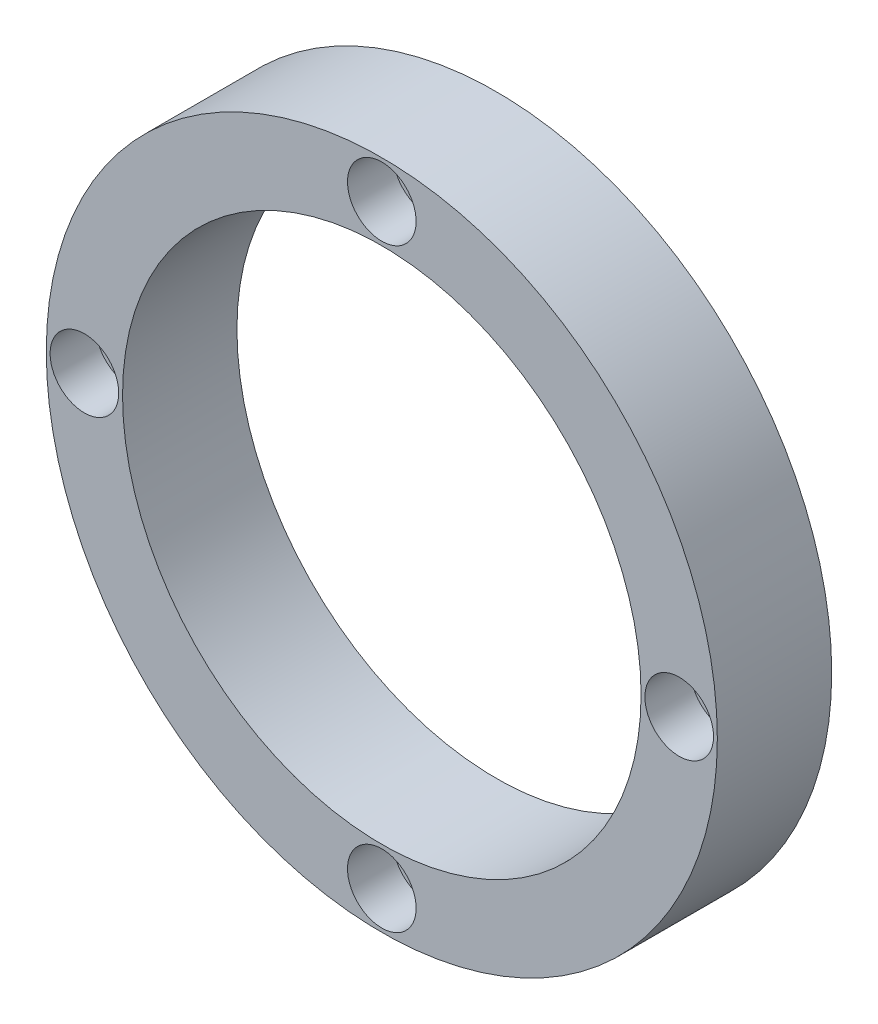
SolidWorks part; units mm, degrees
ref_plane "前视基准面" through (0, 0, 0) normal (0, 0, 1) x (1, 0, 0)
ref_plane "上视基准面" through (0, 0, 0) normal (0, 1, 0) x (1, 0, 0)
ref_plane "右视基准面" through (0, 0, 0) normal (1, 0, 0) x (0, 0, -1)
sketch "草图1" plane through (0, 0, 0) normal (0, 0, 1) x (1, 0, 0)
  circle A0 centre (0, 0) radius 34
  circle A1 centre (0, 0) radius 44
  dimension "D1" = 68
  dimension "D2" = 88
extrude "凸台-拉伸1" add sketch "草图1" along normal blind 15
sketch "草图2" plane through (0, 0, 15) normal (0, 0, 1) x (1, 0, 0)
  circle A0 centre (39, 0) radius 4.5
  dimension "D1" = 9
  dimension "D2" = 39
extrude "切除-拉伸1" cut sketch "草图2" against normal blind 6
sketch "草图3" plane through (0, 0, 9) normal (0, 0, 1) x (1, 0, 0)
  circle A0 centre (39, 0) radius 2.5
  dimension "D1" = 5
extrude "切除-拉伸2" cut sketch "草图3" against normal blind 11
pattern_circular "阵列(圆周)1" count 4 over 360 about axis through (0, 0, 0) along (0, 0, 1) of "切除-拉伸1", "切除-拉伸2"
